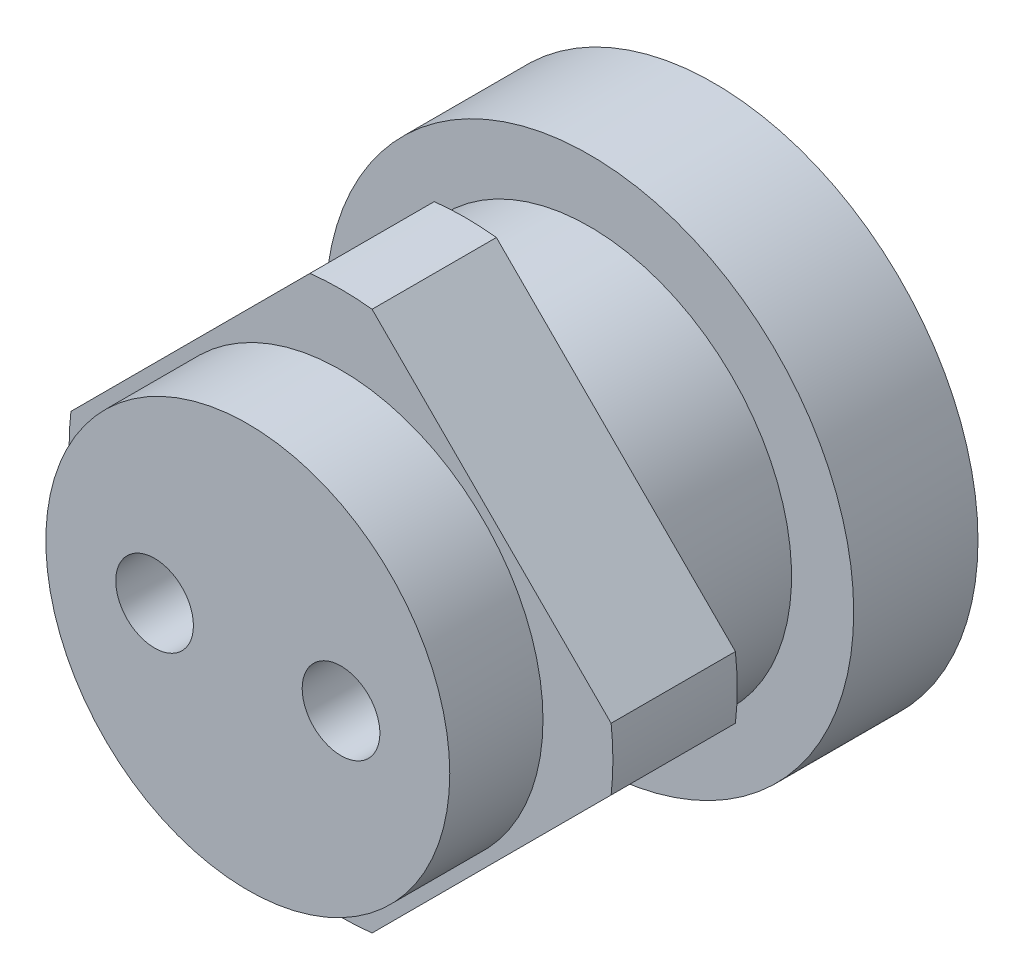
SolidWorks part; units mm, degrees
ref_plane "前视基准面" through (0, 0, 0) normal (0, 0, 1) x (1, 0, 0)
ref_plane "上视基准面" through (0, 0, 0) normal (0, 1, 0) x (1, 0, 0)
ref_plane "右视基准面" through (0, 0, 0) normal (1, 0, 0) x (0, 0, -1)
sketch "草图1" plane through (0, 0, 0) normal (0, 0, 1) x (1, 0, 0)
  circle A0 centre (0, 0) radius 13
  dimension "D1" = 26
extrude "凸台-拉伸1" add sketch "草图1" along normal blind 8
sketch "草图2" plane through (0, 0, 0) normal (0, 0, -1) x (-1, 0, 0)
  circle A0 centre (0, 0) radius 17
  dimension "D1" = 34
extrude "凸台-拉伸2" add sketch "草图2" along normal blind 8
sketch "草图3" plane through (0, 0, 8) normal (0, 0, 1) x (1, 0, 0)
  line L12 (2, 17.3853) -> (17.3853, 2)
  line L14 (17.3853, -2) -> (2, -17.3853)
  line L16 (-2, -17.3853) -> (-17.3853, -2)
  line L18 (-17.3853, 2) -> (-2, 17.3853)
  arc A0 (-17.3853, 2) -> (-17.3853, -2) centre (0, 0) ccw
  arc A1 (-2, -17.3853) -> (2, -17.3853) centre (0, 0) ccw
  arc A2 (17.3853, -2) -> (17.3853, 2) centre (0, 0) ccw
  arc A3 (2, 17.3853) -> (-2, 17.3853) centre (0, 0) ccw
  dimension "D1" = 35
extrude "凸台-拉伸3" add sketch "草图3" along normal blind 8
sketch "草图4" plane through (0, 0, 16) normal (0, 0, 1) x (1, 0, 0)
  circle A0 centre (0, 0) radius 13
  dimension "D1" = 26
extrude "凸台-拉伸4" add sketch "草图4" along normal blind 6
sketch "草图5" plane through (0, 0, -8) normal (0, 0, -1) x (-1, 0, 0)
  circle A0 centre (0, 0) radius 10
  dimension "D1" = 20
extrude "切除-拉伸1" cut sketch "草图5" against normal blind 25
sketch "草图7" plane through (0, 0, 22) normal (0, 0, 1) x (1, 0, 0)
  circle A0 centre (-6, 0) radius 2.5
  dimension "D1" = 5
  dimension "D2" = 6
extrude "切除-拉伸3" cut sketch "草图7" against normal blind 32.5
pattern_circular "阵列(圆周)1" count 2 over 360 about axis through (0, 0, 0) along (0, 0, 1) of "切除-拉伸3"
